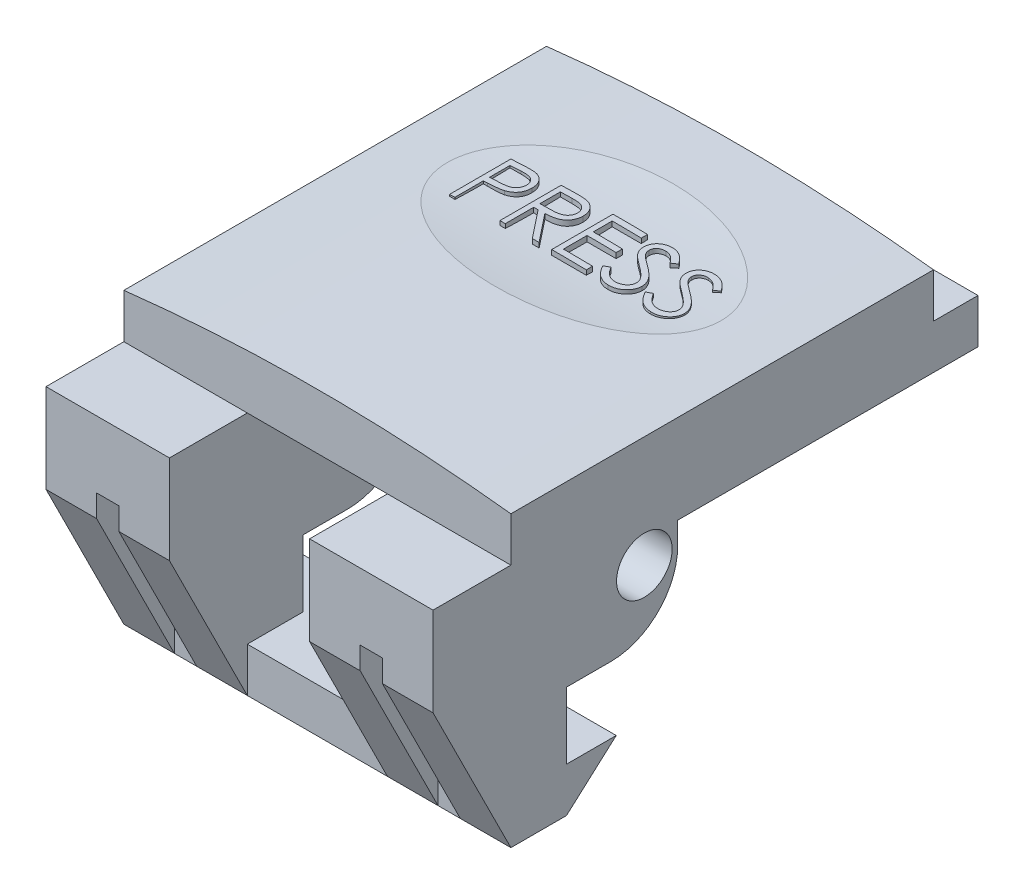
SolidWorks part; units mm, degrees
material "PF"
ref_plane "Front Plane" through (0, 0, 0) normal (0, 0, 1) x (1, 0, 0)
ref_plane "Top Plane" through (0, 0, 0) normal (0, 1, 0) x (1, 0, 0)
ref_plane "Right Plane" through (0, 0, 0) normal (1, 0, 0) x (0, 0, -1)
sketch "Sketch1" plane through (0, 0, 0) normal (0, 1, 0) x (1, 0, 0)
  line L1 (-11.049, -12.065) -> (11.049, -12.065)
  line L2 (-11.049, -12.065) -> (-11.049, 12.065)
  line L3 (-11.049, 12.065) -> (11.049, 12.065)
  line L4 (11.049, -12.065) -> (11.049, 12.065)
  line L5 (-11.049, -12.065) -> (11.049, 12.065) construction
  line L6 (-11.049, 12.065) -> (11.049, -12.065) construction
  point P0 (0, 0)
  dimension "D1" = 22.098
  dimension "D2" = 24.13
extrude "button main" add sketch "Sketch1" against normal blind 2.54
sketch "Sketch2" plane through (0, 0, 0) normal (1, 0, 0) x (0, 0, -1)
  line L0 (12.065, -2.54) -> (12.065, 0) construction
  line L1 (-12.065, -2.54) -> (14.605, -2.54)
  line L2 (-12.065, -16.51) -> (-16.51, -7.62)
  line L3 (-12.065, -16.51) -> (-8.89, -16.51)
  line L4 (14.605, -2.54) -> (14.605, -5.08)
  line L5 (-8.89, -16.51) -> (-6.0502, -13.97)
  line L6 (-6.0502, -13.97) -> (-8.89, -13.97)
  line L7 (-8.89, -13.97) -> (-8.89, -10.16)
  line L8 (14.605, -5.08) -> (-2.54, -5.08)
  line L9 (-2.54, -5.08) -> (-2.54, -6.35)
  line L10 (-8.89, -10.16) -> (-6.35, -10.16)
  line L11 (-16.51, -7.62) -> (-16.51, -2.54)
  line L12 (-12.065, -2.54) -> (-16.51, -2.54)
  arc A0 (-2.54, -6.35) -> (-6.35, -10.16) centre (-6.35, -6.35) cw
  dimension "D1" = 2.54
  dimension "D2" = 2.54
  dimension "D3" = 13.97
  dimension "D4" = 3.175
  dimension "D5" = 3.81
  dimension "D6" = 2.54
  dimension "D7" = 6.35
  dimension "D8" = 5.08
  dimension "D9" = 2.54
  dimension "D10" = 5.08
  dimension "D11" = 4.445
extrude "latch hook" add sketch "Sketch2" along normal up to surface and the other way up to surface up to face at (11.049, -1.27, 0) other way up to face at (-11.049, -1.27, 0)
sketch "Sketch3" plane through (0, 0, 0) normal (0, 0, 1) x (1, 0, 0)
  line L0 (11.049, -2.54) -> (-11.049, -2.54) construction
  line L1 (-4.0005, -13.97) -> (4.0005, -13.97)
  line L2 (-4.0005, -13.97) -> (-4.0005, -2.54)
  line L3 (-4.0005, -2.54) -> (4.0005, -2.54)
  line L4 (4.0005, -13.97) -> (4.0005, -2.54)
  line L5 (-4.0005, -13.97) -> (4.0005, -2.54) construction
  line L6 (-4.0005, -2.54) -> (4.0005, -13.97) construction
  line L7 (11.049, -13.97) -> (-11.049, -13.97) construction
  point P0 (0, -8.255)
  dimension "D1" = 8.001
extrude "center cutout" cut sketch "Sketch3" against normal through all and the other way through all
ref_plane "Plane1" through (0, 0, 16.51) normal (0, 0, 1) x (1, 0, 0)
sketch "Sketch4" plane through (0, 0, 16.51) normal (0, 0, 1) x (1, 0, 0)
  line L1 (11.049, -16.51) -> (-11.049, -16.51) construction
  line L2 (6.8897, -6.35) -> (8.1597, -6.35)
  line L3 (6.8897, -6.35) -> (6.8897, -16.51)
  line L4 (6.8897, -16.51) -> (8.1597, -16.51)
  line L5 (11.049, -2.54) -> (4.0005, -7.62) construction
  line L6 (4.0005, -2.54) -> (11.049, -7.62) construction
  line L7 (-4.0005, -7.62) -> (-11.049, -2.54) construction
  line L8 (-11.049, -7.62) -> (-4.0005, -2.54) construction
  line L9 (8.1597, -6.35) -> (8.1597, -16.51)
  line L10 (6.8897, -6.35) -> (8.1597, -16.51) construction
  line L11 (6.8897, -16.51) -> (8.1597, -6.35) construction
  line L12 (0, -1000) -> (0, 49000) construction
  line L13 (-11.049, 0) -> (11.049, 0) construction
  line L14 (-6.8897, -16.51) -> (-8.1597, -6.35) construction
  line L15 (-6.8897, -6.35) -> (-8.1597, -16.51) construction
  line L16 (-8.1597, -6.35) -> (-8.1597, -16.51)
  line L17 (-6.8897, -16.51) -> (-8.1597, -16.51)
  line L18 (-6.8897, -6.35) -> (-6.8897, -16.51)
  line L19 (-6.8897, -6.35) -> (-8.1597, -6.35)
  line L21 (4.0005, -13.97) -> (-4.0005, -13.97)
  line L22 (4.0005, -13.97) -> (4.0005, -16.51)
  line L23 (4.0005, -16.51) -> (-4.0005, -16.51)
  line L24 (-4.0005, -13.97) -> (-4.0005, -16.51)
  point P0 (7.5247, -11.43)
  point P23 (7.5247, -5.08)
  point P29 (0, 0)
  point P33 (-7.5247, -11.43)
  dimension "D1" = 1.27
  dimension "D2" = 10.16
extrude "backside cutout" cut sketch "Sketch4" against normal up to vertex (5.08 mm away)
sketch "Sketch5" plane through (0, 0, 0) normal (1, 0, 0) x (0, 0, -1)
  circle A0 centre (-4.445, -6.35) radius 1.5875
  dimension "D1" = 3.175
  dimension "D2" = 1.905
  dimension "D3" = 3.81
extrude "latch and spring pin hole" cut sketch "Sketch5" against normal through all and the other way through all
sketch "Sketch8" plane through (0, 0, 0) normal (0, 0, 1) x (1, 0, 0)
  line L0 (-11.049, 0) -> (11.049, 0)
  arc A0 (-11.049, 0) -> (11.049, 0) centre (0, -95.8088) cw
  point P5 (0, 0.635)
  dimension "D1" = 0.635
extrude "rounded top surface" add sketch "Sketch8" along normal up to surface and the other way up to surface up to face at (-1.1748, -2.1167, 12.065) other way up to face at (1.8415, -2.1167, -12.065)
sketch "Sketch11" plane through (0, 0, 0) normal (1, 0, 0) x (0, 0, -1)
  line L0 (-1.905, 0.635) -> (8.255, 0.635)
  line L1 (12.065, 0.635) -> (-12.065, 0.635) construction
  line L2 (12.065, 0) -> (12.065, 0.635) construction
  arc A0 (-1.905, 0.635) -> (8.255, 0.635) centre (3.175, 41.1163) ccw
  point P3 (3.175, 0.3175)
  dimension "D1" = 10.16
  dimension "D2" = 0.3175
  dimension "D3" = 3.81
extrude "PRESS label cutout" cut sketch "Sketch11" against normal mid plane 16.51
sketch "Sketch12" plane through (0, 0, 0) normal (0, 1, 0) x (1, 0, 0)
  text T0 "PRESS"
extrude "PRESS label" add sketch "Sketch12" along normal up to surface (0.4643 mm away)
